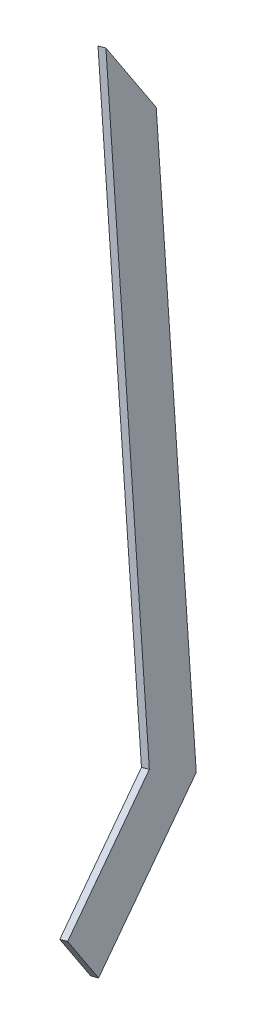
SolidWorks part; units mm, degrees
ref_plane "Front Plane" through (0, 0, 0) normal (0, 0, 1) x (1, 0, 0)
ref_plane "Top Plane" through (0, 0, 0) normal (0, 1, 0) x (1, 0, 0)
ref_plane "Right Plane" through (0, 0, 0) normal (1, 0, 0) x (0, 0, -1)
ref_plane "Plane1" through (-63.5317, -8.3639, 12.7255) normal (0.9725, 0.128, -0.1948) x (0.2331, -0.5341, 0.8126)
sketch "Sketch1" plane through (-63.5317, -8.3639, 12.7255) normal (0.9725, 0.128, -0.1948) x (0.2331, -0.5341, 0.8126)
  line L0 (290.7345, 269.4716) -> (290.7345, 310.0783)
  line L1 (290.7345, 269.4716) -> (446.7605, 469.1757)
  line L2 (290.7345, 310.0783) -> (434.5671, 494.1757)
  line L4 (290.7345, 267.9716) -> (290.7345, 514.1757) construction
  line L5 (40.4214, 267.9716) -> (1012.8768, 267.9716) construction
  line L6 (779.7876, 267.9716) -> (-192.6678, 267.9716) construction
  line L7 (446.7605, 410.8725) -> (446.7605, 469.1757) construction
  line L11 (509.2605, 388.6757) -> (509.2605, 368.6757) construction
  line L12 (434.5671, 494.1757) -> (509.2605, 494.1757)
  line L14 (446.7605, 469.1757) -> (509.2605, 469.1757)
  line L15 (509.2605, 494.1757) -> (509.2605, 469.1757)
  line L17 (449.2605, 388.6757) -> (449.2605, 368.6757) construction
  dimension "D1" = 201.2042
  dimension "D2" = 25
  dimension "D3" = 2.5
  dimension "D4" = 38
  dimension "D5" = 1.5
  dimension "D6" = 25
extrude "Boss-Extrude1" add sketch "Sketch1" against normal blind 3
